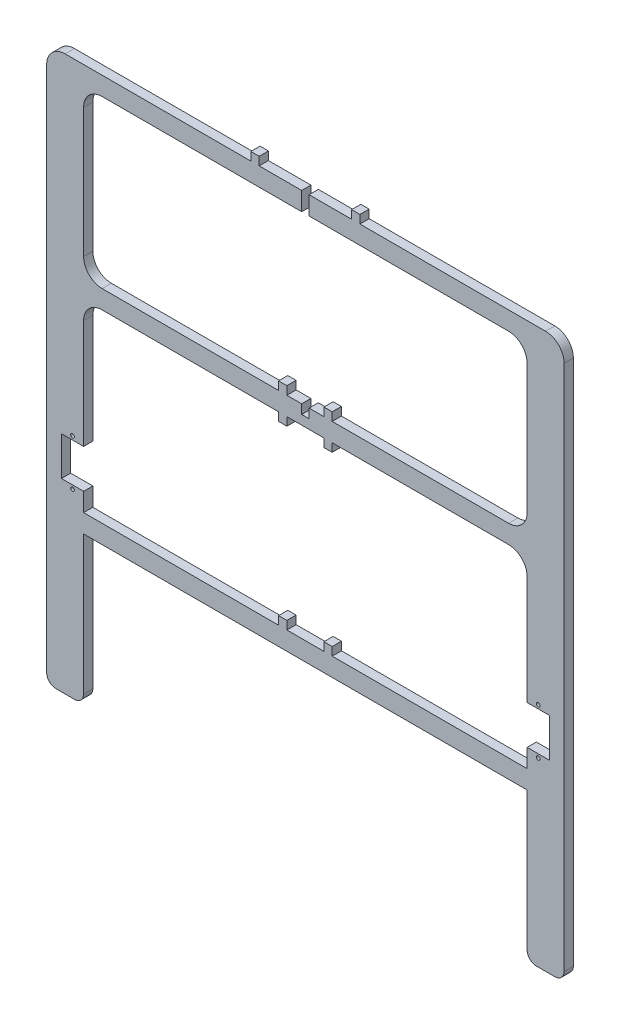
SolidWorks part; units mm, degrees
ref_plane "Front Plane" through (0, 0, 0) normal (0, 0, 1) x (1, 0, 0)
ref_plane "Top Plane" through (0, 0, 0) normal (0, 1, 0) x (1, 0, 0)
ref_plane "Right Plane" through (0, 0, 0) normal (1, 0, 0) x (0, 0, -1)
sketch "Sketch1" plane through (0, 0, 0) normal (0, 0, 1) x (1, 0, 0)
  line L0 (-120, -20) -> (-120, -79)
  line L1 (-130, 100) -> (-120, 100)
  line L2 (-140, 90) -> (-140, -195)
  line L3 (-135, -200) -> (-125, -200)
  line L4 (-120, 80) -> (-120, 10)
  line L5 (-120, 100) -> (-2, 100)
  line L6 (-120, -100) -> (-120, -195)
  line L7 (-110, 90) -> (-2, 90)
  line L8 (-2, 100) -> (-2, 90)
  line L9 (-110, 0) -> (-2, 0)
  line L10 (-132, -79) -> (-120, -79)
  line L11 (-110, -10) -> (0, -10)
  line L12 (0, -5) -> (0, -10)
  line L13 (-132, -79) -> (-132, -100)
  line L14 (-2, 0) -> (-2, -5)
  line L15 (-2, -5) -> (0, -5)
  line L16 (-132, -100) -> (-120, -100)
  line L17 (-10, -14.5) -> (-10, -10)
  line L18 (-120, -110) -> (0, -110)
  line L19 (-120, -110) -> (-120, -120)
  line L20 (-120, -120) -> (0, -120)
  line L21 (0, -110) -> (0, -120)
  line L22 (-29.5, 104.5) -> (-25, 104.5)
  line L23 (-29.5, 104.5) -> (-29.5, 100)
  line L24 (-29.5, 100) -> (-25, 100)
  line L25 (-25, 104.5) -> (-25, 100)
  line L26 (-14.5, 4.5) -> (-10, 4.5)
  line L27 (-14.5, 4.5) -> (-14.5, 0)
  line L28 (-14.5, 0) -> (-10, 0)
  line L29 (-10, 4.5) -> (-10, 0)
  line L30 (-14.5, -10) -> (-10, -10)
  line L31 (-14.5, -14.5) -> (-14.5, -10)
  line L32 (-14.5, -14.5) -> (-10, -14.5)
  line L33 (-132, -89.5) -> (-120, -89.5) construction
  line L35 (-14.5, -105.5) -> (-10, -105.5)
  line L36 (-14.5, -105.5) -> (-14.5, -110)
  line L37 (-14.5, -110) -> (-10, -110)
  line L38 (-10, -105.5) -> (-10, -110)
  arc A0 (-130, 100) -> (-140, 90) centre (-130, 90) ccw
  arc A1 (-120, 80) -> (-110, 90) centre (-110, 80) cw
  arc A2 (-110, 0) -> (-120, 10) centre (-110, 10) cw
  arc A3 (-120, -20) -> (-110, -10) centre (-110, -20) cw
  arc A4 (-125, -200) -> (-120, -195) centre (-125, -195) ccw
  arc A5 (-140, -195) -> (-135, -200) centre (-135, -195) ccw
  circle A6 centre (-126, -77) radius 1
  circle A7 centre (-126, -102) radius 1
  point P16 (-140, 100)
  point P27 (-140, -200)
  dimension "D13" = 10
  dimension "D14" = 10
  dimension "D15" = 10
  dimension "D16" = 10
  dimension "D17" = 5
  dimension "D30" = 2
  dimension "D1" = 300
  dimension "D2" = 20
  dimension "D3" = 10
  dimension "D4" = 120
  dimension "D5" = 10
  dimension "D6" = 100
  dimension "D7" = 2
  dimension "D8" = 0
  dimension "D9" = 0
  dimension "D10" = 5
  dimension "D11" = 2
  dimension "D12" = 20
  dimension "D18" = 12
  dimension "D19" = 21
  dimension "D20" = 100
  dimension "D21" = 10
  dimension "D22" = 0
  dimension "D23" = 80
  dimension "D24" = 4.5
  dimension "D25" = 4.5
  dimension "D26" = 25
  dimension "D27" = 4.5
  dimension "D28" = 4.5
  dimension "D29" = 10
  dimension "D31" = 2
  dimension "D32" = 6
  dimension "D33" = 10.5
  dimension "D34" = 4.5
  dimension "D35" = 4.5
  dimension "D36" = 10
extrude "Boss-Extrude1" add sketch "Sketch1" along normal mid plane 5 contours L2 A5 L3 A4 L6 L16 L13 L10 L0 A3 L11 L12 L15 L14 L9 A2 L4 A1 L7 L8 L5 L1 A0 A6 A7 | L21 L18 L6 L20 | L38 L35 L36 L18 | L29 L26 L27 L9 | L31 L32 L17 L11 | L23 L24 L25 L22
mirror "Mirror1" about plane through (0, 0, 0) normal (1, 0, 0) of "Boss-Extrude1"
equation "\"D32@Sketch1\"=(\"D18@Sketch1\")/2"
equation "\"D33@Sketch1\"=(\"D19@Sketch1\")/2"
equation "\"D34@Sketch1\"=\"D27@Sketch1\""
equation "\"D35@Sketch1\"=\"D28@Sketch1\""
equation "\"D36@Sketch1\"=\"D29@Sketch1\""
